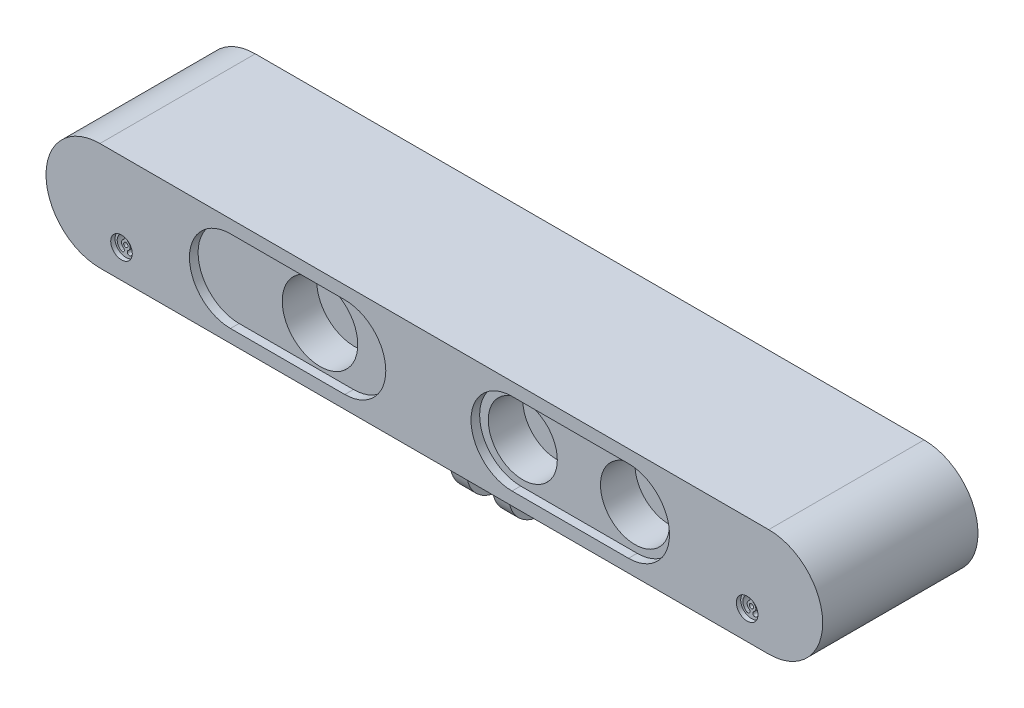
SolidWorks part; units mm, degrees
material "ABS generico"
ref_plane "Front Plane" through (0, 0, 0) normal (0, 0, 1) x (1, 0, 0)
ref_plane "Top Plane" through (0, 0, 0) normal (0, 1, 0) x (1, 0, 0)
ref_plane "Right Plane" through (0, 0, 0) normal (1, 0, 0) x (0, 0, -1)
sketch "Sketch1" plane through (0, 0, 0) normal (0, 0, 1) x (1, 0, 0)
  line L0 (-77.5, 0) -> (77.5, 0) construction
  line L1 (-77.5, 12.5) -> (77.5, 12.5)
  line L2 (-77.5, -12.5) -> (77.5, -12.5)
  arc A0 (-77.5, 12.5) -> (-77.5, -12.5) centre (-77.5, 0) ccw
  arc A1 (77.5, -12.5) -> (77.5, 12.5) centre (77.5, 0) ccw
  point P3 (0, 0)
  dimension "D1" = 12.5
  dimension "D3" = 0
  dimension "D2" = 155
extrude "Boss-Extrude1" add sketch "Sketch1" against normal blind 36
sketch "Sketch3" plane through (0, 0, 0) normal (0, 0, 1) x (1, 0, 0)
  circle A0 centre (-28.5, 0) radius 8.75
  circle A1 centre (18.5, 0) radius 8
  circle A2 centre (44.5, 0) radius 8
  dimension "D1" = 17.5
  dimension "D4" = 16
  dimension "D7" = 16
  dimension "D2" = 28.5
  dimension "D3" = 0
  dimension "D5" = 47
  dimension "D6" = 73
  dimension "D8" = 0
  dimension "D9" = 0
extrude "Cut-Extrude1" cut sketch "Sketch3" against normal blind 10
sketch "Sketch4" plane through (0, 0, 0) normal (0, 0, 1) x (1, 0, 0)
  line L0 (-47.25, 0) -> (-20.75, 0) construction
  line L1 (-47.25, 9.5) -> (-20.75, 9.5)
  line L2 (-47.25, -9.5) -> (-20.75, -9.5)
  line L3 (18, 0) -> (45, 0) construction
  line L4 (18, 9.5) -> (45, 9.5)
  line L5 (18, -9.5) -> (45, -9.5)
  arc A0 (-47.25, 9.5) -> (-47.25, -9.5) centre (-47.25, 0) ccw
  arc A1 (-20.75, -9.5) -> (-20.75, 9.5) centre (-20.75, 0) ccw
  arc A2 (18, 9.5) -> (18, -9.5) centre (18, 0) ccw
  arc A3 (45, -9.5) -> (45, 9.5) centre (45, 0) ccw
  point P3 (-34, 0)
  point P8 (31.5, 0)
  dimension "D1" = 9.5
  dimension "D2" = 9.5
  dimension "D6" = 31.5
  dimension "D3" = 26.5
  dimension "D4" = 34
  dimension "D5" = 27
extrude "Cut-Extrude2" cut sketch "Sketch4" against normal blind 2
sketch "Sketch5" plane through (0, 0, 0) normal (0, 0, 1) x (1, 0, 0)
  circle A0 centre (72.5, -5.8596) radius 2.5
  circle A1 centre (-72.5, -5.8596) radius 2.5
  dimension "D1" = 5
  dimension "D2" = 5
  dimension "D3" = 72.5
  dimension "D4" = 72.5
extrude "Cut-Extrude3" cut sketch "Sketch5" against normal blind 1
sketch "Sketch6" plane through (0, 0, 0) normal (0, 0, 1) x (1, 0, 0)
  circle A0 centre (-72.5, -5.8596) radius 0.5
  circle A1 centre (72.5, -5.8596) radius 0.5
  arc A2 (-71.6708, -4.6096) -> (-71.6708, -7.1096) centre (-72.5, -5.8596) cw construction
  arc A3 (-71.3945, -7.5262) -> (-71.3945, -4.1929) centre (-72.5, -5.8596) ccw
  arc A4 (-71.9472, -6.6929) -> (-71.9472, -5.0262) centre (-72.5, -5.8596) ccw
  arc A5 (-71.9472, -6.6929) -> (-71.3945, -7.5262) centre (-71.6708, -7.1096) ccw
  arc A6 (-71.3945, -4.1929) -> (-71.9472, -5.0262) centre (-71.6708, -4.6096) ccw
  arc A7 (-73.3292, -4.6096) -> (-73.3292, -7.1096) centre (-72.5, -5.8596) ccw construction
  arc A8 (-73.6055, -4.1929) -> (-73.6055, -7.5262) centre (-72.5, -5.8596) ccw
  arc A9 (-73.0528, -5.0262) -> (-73.0528, -6.6929) centre (-72.5, -5.8596) ccw
  arc A10 (-73.0528, -5.0262) -> (-73.6055, -4.1929) centre (-73.3292, -4.6096) ccw
  arc A11 (-73.6055, -7.5262) -> (-73.0528, -6.6929) centre (-73.3292, -7.1096) ccw
  arc A12 (73.3292, -4.6096) -> (73.3292, -7.1096) centre (72.5, -5.8596) cw construction
  arc A13 (73.6055, -7.5262) -> (73.6055, -4.1929) centre (72.5, -5.8596) ccw
  arc A14 (73.0528, -6.6929) -> (73.0528, -5.0262) centre (72.5, -5.8596) ccw
  arc A15 (73.0528, -6.6929) -> (73.6055, -7.5262) centre (73.3292, -7.1096) ccw
  arc A16 (73.6055, -4.1929) -> (73.0528, -5.0262) centre (73.3292, -4.6096) ccw
  arc A17 (71.6708, -4.6096) -> (71.6708, -7.1096) centre (72.5, -5.8596) ccw construction
  arc A18 (71.3945, -4.1929) -> (71.3945, -7.5262) centre (72.5, -5.8596) ccw
  arc A19 (71.9472, -5.0262) -> (71.9472, -6.6929) centre (72.5, -5.8596) ccw
  arc A20 (71.9472, -5.0262) -> (71.3945, -4.1929) centre (71.6708, -4.6096) ccw
  arc A21 (71.3945, -7.5262) -> (71.9472, -6.6929) centre (71.6708, -7.1096) ccw
  circle A22 centre (72.5, -5.8596) radius 2.5 construction
  point P8 (-71, -5.8596)
  point P16 (-74, -5.8596)
  point P23 (74, -5.8596)
  point P31 (71, -5.8596)
  dimension "D2" = 1
  dimension "D5" = 0.5
  dimension "D6" = 2.5
  dimension "D9" = 0.5
  dimension "D11" = 1
  dimension "D14" = 0.5
  dimension "D18" = 0.5
  dimension "D3" = 0
  dimension "D4" = 1.5
  dimension "D7" = 0
  dimension "D8" = 2.5
  dimension "D10" = 1.5
  dimension "D12" = 0
  dimension "D13" = 1.5
  dimension "D15" = 2.5
  dimension "D16" = 0
  dimension "D17" = 2.5
  dimension "D19" = 1.5
  dimension "D21" = 0
extrude "Cut-Extrude4" cut sketch "Sketch6" against normal blind 5
sketch "Sketch7" plane through (0, -12.5, 0) normal (0, -1, 0) x (1, 0, 0)
  line L0 (-77.5, 0) -> (77.5, 0) construction
  line L1 (3, -10.5) -> (6.8, -10.5)
  line L2 (3, -10.5) -> (3, -25.5)
  line L3 (3, -25.5) -> (6.8, -25.5)
  line L4 (6.8, -10.5) -> (6.8, -25.5)
  line L6 (-3, -10.5) -> (-6.8, -10.5)
  line L7 (-3, -10.5) -> (-3, -25.5)
  line L8 (-3, -25.5) -> (-6.8, -25.5)
  line L9 (-6.8, -10.5) -> (-6.8, -25.5)
  dimension "D1" = 3.8
  dimension "D2" = 15
  dimension "D3" = 10.5
  dimension "D4" = 3
  dimension "D5" = 3.8
  dimension "D6" = 15
  dimension "D7" = 3
  dimension "D8" = 10.5
extrude "Boss-Extrude2" add sketch "Sketch7" along normal blind 17
sketch "Sketch8" plane through (-6.8, 0, 0) normal (-1, 0, 0) x (0, 0, 1)
  line L0 (-10.5, -29.5) -> (-10.5, -12.5) construction
  line L1 (-25.5, -29.5) -> (-25.5, -12.5) construction
  line L2 (-10.5, -21) -> (-7.9034, -21)
  line L3 (-7.9034, -21) -> (-7.606, -33.9286)
  line L4 (-7.606, -33.9286) -> (-27.6037, -34.3885)
  line L5 (-27.6037, -34.3885) -> (-27.6037, -21)
  line L6 (-27.6037, -21) -> (-25.5, -21)
  arc A0 (-10.5, -21) -> (-25.5, -21) centre (-18, -21.4844) cw
  circle A1 centre (-18, -21.4844) radius 2.5
extrude "Cut-Extrude5" cut sketch "Sketch8" along normal through all and the other way through all
sketch "Schizzo2" plane through (0, 0, 0) normal (1, 0, 0) x (0, 0, -1)
  line L0 (0, 0) -> (-8000, 3313.7085) construction
  line L1 (0, 0) -> (-8000, -3313.7085) construction
  line L2 (-8000, 3313.7085) -> (-8000, -3313.7085) construction
  line L3 (-8000, 0) -> (0, 0) construction
  line L4 (36, -12.5) -> (0, -12.5) construction
  line L5 (-450, -186.3961) -> (-450, 186.3961) construction
  dimension "D1" = 45
  dimension "D2" = 450
  dimension "D3" = 8000
